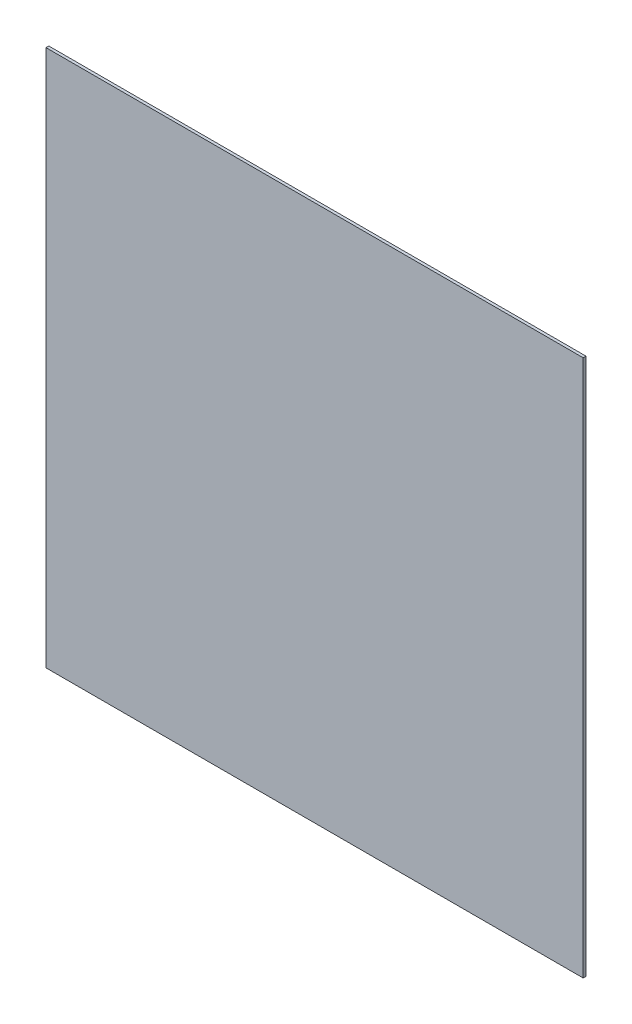
SolidWorks part; units mm, degrees
ref_plane "Front Plane" through (0, 0, 0) normal (0, 0, 1) x (1, 0, 0)
ref_plane "Top Plane" through (0, 0, 0) normal (0, 1, 0) x (1, 0, 0)
ref_plane "Right Plane" through (0, 0, 0) normal (1, 0, 0) x (0, 0, -1)
sketch "Sketch1" plane through (0, 0, 0) normal (0, 0, 1) x (1, 0, 0)
  line L1 (-474, 474) -> (0, 474)
  line L2 (-474, 474) -> (-474, 0)
  line L3 (-474, 0) -> (0, 0)
  line L4 (0, 474) -> (0, 0)
  dimension "D1" = 474
extrude "Boss-Extrude1" add sketch "Sketch1" along normal blind 2.5
